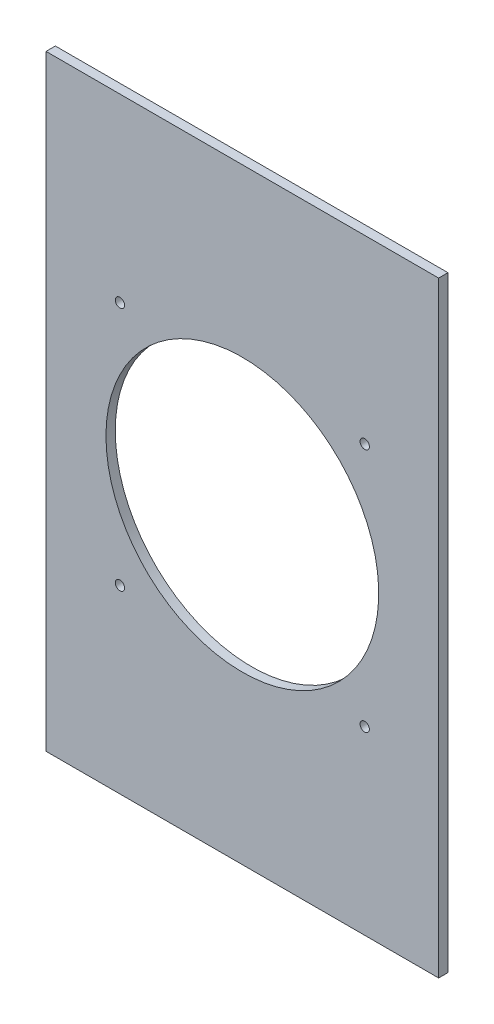
SolidWorks part; units mm, degrees
ref_plane "Спереди" through (0, 0, 0) normal (0, 0, 1) x (1, 0, 0)
ref_plane "Сверху" through (0, 0, 0) normal (0, 1, 0) x (1, 0, 0)
ref_plane "Справа" through (0, 0, 0) normal (1, 0, 0) x (0, 0, -1)
sketch "Sketch1" plane through (0, 0, 0) normal (0, 0, 1) x (1, 0, 0)
  line L0 (-84.2, -130) -> (-84.2, 130) construction
  line L7 (-84.2, -130) -> (84.2, -130)
  line L8 (-84.2, -130) -> (-84.2, 130)
  line L9 (-84.2, 130) -> (84.2, 130)
  line L10 (84.2, -130) -> (84.2, 130)
  line L15 (-84.2, -130) -> (84.2, 130) construction
  line L16 (-84.2, 130) -> (84.2, -130) construction
  line L17 (-88.2, 130) -> (-84.2, 130) construction
  point P0 (0, 0)
extrude "Extrude1" add sketch "Sketch1" along normal blind 4
sketch "Sketch2" plane through (0, 0, 0) normal (0, 0, 1) x (1, 0, 0)
  circle A0 centre (0, 0) radius 58.5
  circle A1 centre (-52.5, -52.5) radius 2
  circle A2 centre (52.5, -52.5) radius 2
  circle A3 centre (52.5, 52.5) radius 2
  circle A4 centre (-52.5, 52.5) radius 2
  point P1 (52.5, -52.5)
  point P13 (-52.5, -52.5)
  point P14 (52.5, 52.5)
  point P15 (-52.5, 52.5)
  dimension "D1" = 4
  dimension "D2" = 117
extrude "Cut-Extrude5" cut sketch "Sketch2" along normal up to vertex (4 mm away)
equation "\"thickness\"=4"
equation "\"D1@Extrude1\"=\"thickness\""
